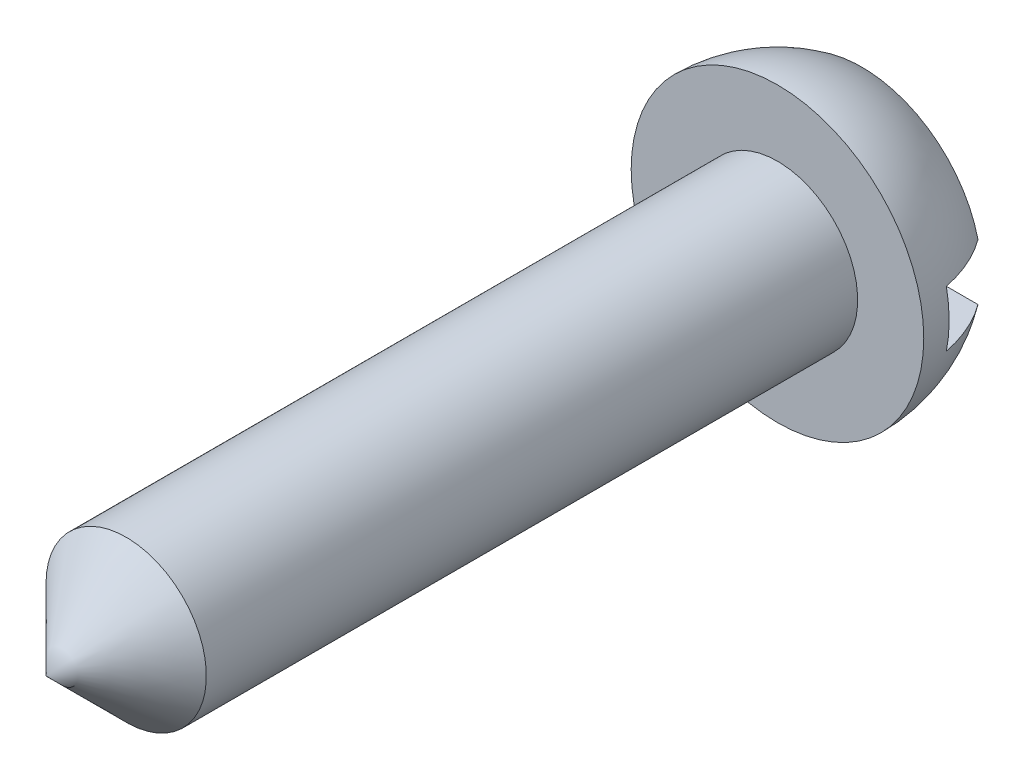
SolidWorks part; units mm, degrees
ref_plane "Plano frontal" through (0, 0, 0) normal (0, 0, 1) x (1, 0, 0)
ref_plane "Plano superior" through (0, 0, 0) normal (0, 1, 0) x (1, 0, 0)
ref_plane "Plano direito" through (0, 0, 0) normal (1, 0, 0) x (0, 0, -1)
sketch "Esboço1" plane through (0, 0, 0) normal (0, 1, 0) x (1, 0, 0)
  line L0 (0, 0) -> (0, 1.5)
  line L1 (0, 1.5) -> (2.1237, 1.5)
  line L2 (1.425, 0) -> (2.6, 0)
  line L3 (0, 0) -> (0, -13)
  line L4 (0, -0.9152) -> (1.425, -0.9152) construction
  line L5 (1.425, 0) -> (1.425, -11.575)
  line L6 (0, -13) -> (1.425, -11.575)
  arc A0 (2.6, 0) -> (2.1237, 1.5) centre (0, 0) ccw
revolve "Revolução1" add sketch "Esboço1" angle 360 about L3
sketch "Esboço2" plane through (0, 0, -1.5) normal (0, 0, -1) x (-1, 0, 0)
  line L1 (-2.9474, 0.5) -> (2.9474, 0.5)
  line L2 (-2.9474, 0.5) -> (-2.9474, -0.5)
  line L3 (-2.9474, -0.5) -> (2.9474, -0.5)
  line L4 (2.9474, 0.5) -> (2.9474, -0.5)
  line L5 (-2.9474, 0.5) -> (2.9474, -0.5) construction
  line L6 (-2.9474, -0.5) -> (2.9474, 0.5) construction
  point P0 (0, 0)
extrude "Corte-extrusão1" cut sketch "Esboço2" against normal blind 1
